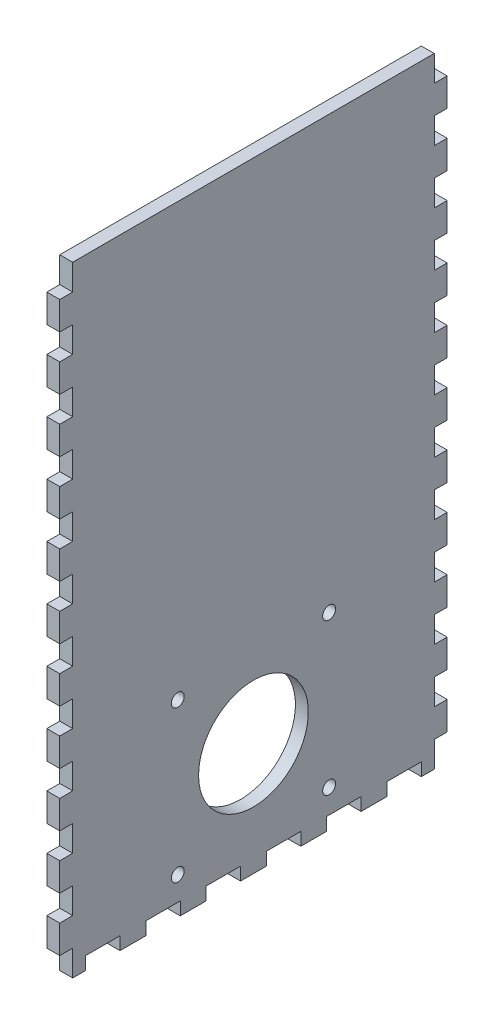
SolidWorks part; units mm, degrees
material "Acrylic (Medium-high impact)"
ref_plane "Front Plane" through (0, 0, 0) normal (0, 0, 1) x (1, 0, 0)
ref_plane "Top Plane" through (0, 0, 0) normal (0, 1, 0) x (1, 0, 0)
ref_plane "Right Plane" through (0, 0, 0) normal (1, 0, 0) x (0, 0, -1)
sketch "Sketch1" plane through (0, 0, 0) normal (0, 1, 0) x (1, 0, 0)
  line L1 (-254, 95.25) -> (254, 95.25)
  line L2 (-254, 95.25) -> (-254, -95.25)
  line L3 (-254, -95.25) -> (254, -95.25)
  line L4 (254, 95.25) -> (254, -95.25)
  point P4 (-254, 0)
  point P6 (0, 95.25)
  dimension "D1" = 190.5
  dimension "D2" = 508
extrude "Boss-Extrude1" add sketch "Sketch1" along normal blind 6.35
sketch "Sketch2" plane through (0, 6.35, 0) normal (0, 1, 0) x (1, 0, 0)
  line L0 (254, -95.25) -> (254, 95.25) construction
  line L1 (-254, 95.25) -> (254, 95.25)
  line L2 (-254, 95.25) -> (-254, -95.25)
  line L3 (-254, -95.25) -> (254, -95.25)
  line L4 (254, 95.25) -> (254, -95.25)
  line L5 (-254, -95.25) -> (254, -95.25) construction
  line L7 (-247.65, 88.9) -> (247.65, 88.9)
  line L8 (-247.65, 88.9) -> (-247.65, -88.9)
  line L9 (-247.65, -88.9) -> (247.65, -88.9)
  line L10 (247.65, 88.9) -> (247.65, -88.9)
  point P7 (-247.65, 0)
  point P14 (-254, 0)
  point P15 (0, -88.9)
  point P16 (0, -95.25)
  point P17 (247.65, 0)
  point P18 (254, 0)
  dimension "D1" = 6.35
  dimension "D2" = 6.35
extrude "Boss-Extrude2" add sketch "Sketch2" along normal blind 298.45
sketch "Sketch3" plane through (0, 0, 95.25) normal (0, 0, 1) x (1, 0, 0)
  line L0 (0, 304.8) -> (0, 0) construction
  line L1 (-254, 304.8) -> (254, 304.8) construction
  line L2 (-247.65, 6.35) -> (247.65, 6.35) construction
  line L4 (-3.302, 283.21) -> (-3.302, 6.35)
  line L5 (-3.302, 6.35) -> (3.302, 6.35)
  line L6 (3.302, 292.354) -> (3.302, 6.35)
  line L7 (3.302, 292.354) -> (-16.256, 292.354)
  line L9 (-5.842, 285.75) -> (-16.256, 285.75)
  line L10 (-16.256, 292.354) -> (-16.256, 285.75)
  line L11 (3.302, 101.6) -> (16.002, 101.6) construction
  line L12 (-254, 0) -> (254, 0) construction
  line L13 (12.827, 88.9) -> (12.827, 101.6) construction
  line L14 (9.652, 88.9) -> (16.002, 88.9)
  line L15 (9.652, 88.9) -> (9.652, 71.9667)
  line L16 (9.652, 71.9667) -> (16.002, 71.9667)
  line L17 (16.002, 88.9) -> (16.002, 71.9667)
  line L18 (9.652, 42.3333) -> (16.002, 42.3333)
  line L19 (9.652, 42.3333) -> (9.652, 59.2667)
  line L20 (9.652, 59.2667) -> (16.002, 59.2667)
  line L21 (16.002, 42.3333) -> (16.002, 59.2667)
  line L26 (9.652, 29.6333) -> (16.002, 29.6333)
  line L27 (9.652, 29.6333) -> (9.652, 12.7)
  line L28 (9.652, 12.7) -> (16.002, 12.7)
  line L29 (16.002, 29.6333) -> (16.002, 12.7)
  line L30 (12.827, 59.2667) -> (12.827, 71.9667) construction
  line L31 (12.827, 29.6333) -> (12.827, 42.3333) construction
  line L32 (12.827, 12.7) -> (12.827, 0) construction
  arc A0 (-3.302, 283.21) -> (-5.842, 285.75) centre (-5.842, 283.21) ccw
  point P5 (0, 6.35)
  dimension "D5" = 2.54
  dimension "D1" = 6.604
  dimension "D2" = 12.954
  dimension "D3" = 6.604
  dimension "D4" = 286.004
  dimension "D6" = 101.6
  dimension "D7" = 12.7
  dimension "D8" = 12.7
  dimension "D9" = 6.35
extrude "Cut-Extrude1" cut sketch "Sketch3" against normal blind 12.7
sketch "Sketch4" plane through (0, 0, -88.9) normal (0, 0, 1) x (1, 0, 0)
  line L0 (-254, 304.8) -> (254, 304.8) construction
  line L1 (-22.606, 304.8) -> (-16.256, 304.8)
  line L2 (-22.606, 304.8) -> (-22.606, 6.35)
  line L3 (-22.606, 6.35) -> (-16.256, 6.35)
  line L4 (-16.256, 304.8) -> (-16.256, 6.35)
  line L5 (6.477, 263.525) -> (6.477, 247.65) construction
  line L6 (-16.256, 292.354) -> (-16.256, 285.75) construction
  line L7 (3.302, 304.8) -> (9.652, 304.8)
  line L8 (3.302, 304.8) -> (3.302, 6.35)
  line L9 (3.302, 6.35) -> (9.652, 6.35)
  line L10 (9.652, 304.8) -> (9.652, 6.35)
  line L11 (247.65, 6.35) -> (-247.65, 6.35) construction
  line L12 (3.302, 6.35) -> (3.302, 292.354) construction
  line L13 (-16.256, 304.8) -> (-22.606, 304.8)
  line L14 (-16.256, 304.8) -> (-16.256, 292.1)
  line L15 (-16.256, 292.1) -> (-22.606, 292.1)
  line L16 (-22.606, 304.8) -> (-22.606, 292.1)
  line L17 (-16.256, 276.225) -> (-22.606, 276.225)
  line L18 (-16.256, 276.225) -> (-16.256, 263.525)
  line L19 (-16.256, 263.525) -> (-22.606, 263.525)
  line L20 (-22.606, 276.225) -> (-22.606, 263.525)
  line L21 (-22.606, 6.35) -> (-16.256, 6.35)
  line L22 (-22.606, 6.35) -> (-22.606, 19.05)
  line L23 (-22.606, 19.05) -> (-16.256, 19.05)
  line L24 (-16.256, 6.35) -> (-16.256, 19.05)
  line L25 (-22.606, 34.925) -> (-16.256, 34.925)
  line L26 (-22.606, 34.925) -> (-22.606, 47.625)
  line L27 (-22.606, 47.625) -> (-16.256, 47.625)
  line L28 (-16.256, 34.925) -> (-16.256, 47.625)
  line L29 (-22.606, 92.075) -> (-16.256, 92.075)
  line L30 (-22.606, 92.075) -> (-22.606, 104.775)
  line L31 (-22.606, 104.775) -> (-16.256, 104.775)
  line L32 (-16.256, 92.075) -> (-16.256, 104.775)
  line L33 (-22.606, 149.225) -> (-16.256, 149.225)
  line L34 (-22.606, 149.225) -> (-22.606, 161.925)
  line L35 (-22.606, 161.925) -> (-16.256, 161.925)
  line L36 (-16.256, 149.225) -> (-16.256, 161.925)
  line L37 (-22.606, 177.8) -> (-16.256, 177.8)
  line L38 (-22.606, 177.8) -> (-22.606, 190.5)
  line L39 (-22.606, 190.5) -> (-16.256, 190.5)
  line L40 (-16.256, 177.8) -> (-16.256, 190.5)
  line L41 (-22.606, 206.375) -> (-16.256, 206.375)
  line L42 (-22.606, 206.375) -> (-22.606, 219.075)
  line L43 (-22.606, 219.075) -> (-16.256, 219.075)
  line L44 (-16.256, 206.375) -> (-16.256, 219.075)
  line L45 (-22.606, 234.95) -> (-16.256, 234.95)
  line L46 (-22.606, 234.95) -> (-22.606, 247.65)
  line L47 (-22.606, 247.65) -> (-16.256, 247.65)
  line L48 (-16.256, 234.95) -> (-16.256, 247.65)
  line L49 (-16.256, 133.35) -> (-22.606, 133.35)
  line L50 (-16.256, 133.35) -> (-16.256, 120.65)
  line L51 (-16.256, 120.65) -> (-22.606, 120.65)
  line L52 (-22.606, 133.35) -> (-22.606, 120.65)
  line L53 (-16.256, 76.2) -> (-22.606, 76.2)
  line L54 (-16.256, 76.2) -> (-16.256, 63.5)
  line L55 (-16.256, 63.5) -> (-22.606, 63.5)
  line L56 (-22.606, 76.2) -> (-22.606, 63.5)
  line L57 (-19.431, 304.8) -> (-19.431, 292.1) construction
  line L58 (-19.431, 292.1) -> (-19.431, 276.225) construction
  line L59 (-19.431, 276.225) -> (-19.431, 263.525) construction
  line L60 (-19.431, 247.65) -> (-19.431, 234.95) construction
  line L61 (-19.431, 234.95) -> (-19.431, 219.075) construction
  line L62 (-19.431, 219.075) -> (-19.431, 206.375) construction
  line L63 (-19.431, 206.375) -> (-19.431, 190.5) construction
  line L64 (-19.431, 190.5) -> (-19.431, 177.8) construction
  line L65 (-19.431, 177.8) -> (-19.431, 161.925) construction
  line L66 (-19.431, 161.925) -> (-19.431, 149.225) construction
  line L67 (-19.431, 133.35) -> (-19.431, 120.65) construction
  line L68 (-19.431, 120.65) -> (-19.431, 104.775) construction
  line L69 (-19.431, 104.775) -> (-19.431, 92.075) construction
  line L70 (-19.431, 92.075) -> (-19.431, 76.2) construction
  line L71 (-19.431, 76.2) -> (-19.431, 63.5) construction
  line L72 (-19.431, 63.5) -> (-19.431, 47.625) construction
  line L73 (-19.431, 47.625) -> (-19.431, 34.925) construction
  line L74 (-19.431, 34.925) -> (-19.431, 19.05) construction
  line L75 (-19.431, 19.05) -> (-19.431, 6.35) construction
  line L76 (-19.431, 149.225) -> (-19.431, 133.35) construction
  line L77 (-19.431, 263.525) -> (-19.431, 247.65) construction
  line L78 (-6.477, 304.8) -> (-6.477, 0) construction
  line L79 (254, 304.8) -> (-254, 304.8) construction
  line L80 (254, 0) -> (-254, 0) construction
  line L81 (-6.477, 8.3493) -> (3.302, 8.3493) construction
  line L82 (-6.477, 8.3493) -> (-16.256, 8.3493) construction
  line L83 (6.477, 149.225) -> (6.477, 133.35) construction
  line L84 (6.477, 19.05) -> (6.477, 6.35) construction
  line L85 (6.477, 34.925) -> (6.477, 19.05) construction
  line L86 (6.477, 47.625) -> (6.477, 34.925) construction
  line L87 (6.477, 63.5) -> (6.477, 47.625) construction
  line L88 (6.477, 76.2) -> (6.477, 63.5) construction
  line L89 (6.477, 92.075) -> (6.477, 76.2) construction
  line L90 (6.477, 104.775) -> (6.477, 92.075) construction
  line L91 (6.477, 120.65) -> (6.477, 104.775) construction
  line L92 (6.477, 133.35) -> (6.477, 120.65) construction
  line L93 (6.477, 161.925) -> (6.477, 149.225) construction
  line L94 (6.477, 177.8) -> (6.477, 161.925) construction
  line L95 (6.477, 190.5) -> (6.477, 177.8) construction
  line L96 (6.477, 206.375) -> (6.477, 190.5) construction
  line L97 (6.477, 219.075) -> (6.477, 206.375) construction
  line L98 (6.477, 234.95) -> (6.477, 219.075) construction
  line L99 (6.477, 247.65) -> (6.477, 234.95) construction
  line L100 (6.477, 276.225) -> (6.477, 263.525) construction
  line L101 (6.477, 292.1) -> (6.477, 276.225) construction
  line L102 (6.477, 304.8) -> (6.477, 292.1) construction
  line L103 (9.652, 76.2) -> (9.652, 63.5)
  line L104 (3.302, 63.5) -> (9.652, 63.5)
  line L105 (3.302, 76.2) -> (3.302, 63.5)
  line L106 (3.302, 76.2) -> (9.652, 76.2)
  line L107 (9.652, 133.35) -> (9.652, 120.65)
  line L108 (3.302, 120.65) -> (9.652, 120.65)
  line L109 (3.302, 133.35) -> (3.302, 120.65)
  line L110 (3.302, 133.35) -> (9.652, 133.35)
  line L111 (3.302, 234.95) -> (3.302, 247.65)
  line L112 (9.652, 247.65) -> (3.302, 247.65)
  line L113 (9.652, 234.95) -> (9.652, 247.65)
  line L114 (9.652, 234.95) -> (3.302, 234.95)
  line L115 (3.302, 206.375) -> (3.302, 219.075)
  line L116 (9.652, 219.075) -> (3.302, 219.075)
  line L117 (9.652, 206.375) -> (9.652, 219.075)
  line L118 (9.652, 206.375) -> (3.302, 206.375)
  line L119 (3.302, 177.8) -> (3.302, 190.5)
  line L120 (9.652, 190.5) -> (3.302, 190.5)
  line L121 (9.652, 177.8) -> (9.652, 190.5)
  line L122 (9.652, 177.8) -> (3.302, 177.8)
  line L123 (3.302, 149.225) -> (3.302, 161.925)
  line L124 (9.652, 161.925) -> (3.302, 161.925)
  line L125 (9.652, 149.225) -> (9.652, 161.925)
  line L126 (9.652, 149.225) -> (3.302, 149.225)
  line L127 (3.302, 92.075) -> (3.302, 104.775)
  line L128 (9.652, 104.775) -> (3.302, 104.775)
  line L129 (9.652, 92.075) -> (9.652, 104.775)
  line L130 (9.652, 92.075) -> (3.302, 92.075)
  line L131 (3.302, 34.925) -> (3.302, 47.625)
  line L132 (9.652, 47.625) -> (3.302, 47.625)
  line L133 (9.652, 34.925) -> (9.652, 47.625)
  line L134 (9.652, 34.925) -> (3.302, 34.925)
  line L135 (3.302, 6.35) -> (3.302, 19.05)
  line L136 (9.652, 19.05) -> (3.302, 19.05)
  line L137 (9.652, 6.35) -> (9.652, 19.05)
  line L138 (9.652, 6.35) -> (3.302, 6.35)
  line L139 (9.652, 276.225) -> (9.652, 263.525)
  line L140 (3.302, 263.525) -> (9.652, 263.525)
  line L141 (3.302, 276.225) -> (3.302, 263.525)
  line L142 (3.302, 276.225) -> (9.652, 276.225)
  line L143 (9.652, 304.8) -> (9.652, 292.1)
  line L144 (3.302, 292.1) -> (9.652, 292.1)
  line L145 (3.302, 304.8) -> (3.302, 292.1)
  line L146 (3.302, 304.8) -> (9.652, 304.8)
  line L147 (3.302, 304.8) -> (3.302, 6.35)
  line L148 (9.652, 6.35) -> (3.302, 6.35)
  line L149 (9.652, 304.8) -> (9.652, 6.35)
  line L150 (9.652, 304.8) -> (3.302, 304.8)
  point P14 (-16.256, 289.052)
  dimension "D1" = 6.35
  dimension "D2" = 12.7
extrude "Cut-Extrude2" cut sketch "Sketch4" against normal up to next (6.35 mm away) contours L17 L4 L15 L2 | L2 L47 L4 L19 | L45 L2 L43 L4 | L41 L2 L39 L4 | L37 L2 L35 L4 | L49 L4 L33 L2 | L4 L51 L2 L31 | L53 L4 L29 L2 | L4 L55 L2 L27 | L25 L2 L23 L4
ref_plane "Plane1" through (-6.477, 0, 0) normal (-1, 0, 0) x (0, 0, 1)
mirror "Mirror1" about plane through (-6.477, 0, 0) normal (-1, 0, 0) of "Cut-Extrude2"
sketch "Sketch5" plane through (0, 0, 0) normal (0, -1, 0) x (-1, 0, 0)
  line L0 (-227.9316, -95.25) -> (-227.9316, -88.9)
  line L1 (-247.65, 88.9) -> (247.65, 88.9)
  line L2 (-247.65, 88.9) -> (-247.65, -88.9)
  line L3 (-247.65, -88.9) -> (247.65, -88.9)
  line L4 (247.65, 88.9) -> (247.65, -88.9)
  line L5 (-254, -95.25) -> (-241.3, -95.25)
  line L6 (-254, -95.25) -> (-254, -88.9)
  line L7 (-254, -88.9) -> (-241.3, -88.9)
  line L8 (-241.3, -95.25) -> (-241.3, -88.9)
  line L9 (-227.9316, -95.25) -> (-215.2316, -95.25)
  line L10 (-227.9316, -88.9) -> (-215.2316, -88.9)
  line L11 (-215.2316, -95.25) -> (-215.2316, -88.9)
  line L12 (-201.8632, -95.25) -> (-201.8632, -88.9)
  line L13 (-201.8632, -95.25) -> (-189.1632, -95.25)
  line L14 (-201.8632, -88.9) -> (-189.1632, -88.9)
  line L15 (-189.1632, -95.25) -> (-189.1632, -88.9)
  line L16 (-175.7947, -95.25) -> (-175.7947, -88.9)
  line L17 (-175.7947, -95.25) -> (-163.0947, -95.25)
  line L18 (-175.7947, -88.9) -> (-163.0947, -88.9)
  line L19 (-163.0947, -95.25) -> (-163.0947, -88.9)
  line L20 (-149.7263, -95.25) -> (-149.7263, -88.9)
  line L21 (-149.7263, -95.25) -> (-137.0263, -95.25)
  line L22 (-149.7263, -88.9) -> (-137.0263, -88.9)
  line L23 (-137.0263, -95.25) -> (-137.0263, -88.9)
  line L24 (-123.6579, -95.25) -> (-123.6579, -88.9)
  line L25 (-123.6579, -95.25) -> (-110.9579, -95.25)
  line L26 (-123.6579, -88.9) -> (-110.9579, -88.9)
  line L27 (-110.9579, -95.25) -> (-110.9579, -88.9)
  line L28 (-97.5895, -95.25) -> (-97.5895, -88.9)
  line L29 (-97.5895, -95.25) -> (-84.8895, -95.25)
  line L30 (-97.5895, -88.9) -> (-84.8895, -88.9)
  line L31 (-84.8895, -95.25) -> (-84.8895, -88.9)
  line L32 (-71.5211, -95.25) -> (-71.5211, -88.9)
  line L33 (-71.5211, -95.25) -> (-58.8211, -95.25)
  line L34 (-71.5211, -88.9) -> (-58.8211, -88.9)
  line L35 (-58.8211, -95.25) -> (-58.8211, -88.9)
  line L36 (-45.4526, -95.25) -> (-45.4526, -88.9)
  line L37 (-45.4526, -95.25) -> (-32.7526, -95.25)
  line L38 (-45.4526, -88.9) -> (-32.7526, -88.9)
  line L39 (-32.7526, -95.25) -> (-32.7526, -88.9)
  line L40 (-19.3842, -95.25) -> (-19.3842, -88.9)
  line L41 (-19.3842, -95.25) -> (-6.6842, -95.25)
  line L42 (-19.3842, -88.9) -> (-6.6842, -88.9)
  line L43 (-6.6842, -95.25) -> (-6.6842, -88.9)
  line L44 (6.6842, -95.25) -> (6.6842, -88.9)
  line L45 (6.6842, -95.25) -> (19.3842, -95.25)
  line L46 (6.6842, -88.9) -> (19.3842, -88.9)
  line L47 (19.3842, -95.25) -> (19.3842, -88.9)
  line L48 (32.7526, -95.25) -> (32.7526, -88.9)
  line L49 (32.7526, -95.25) -> (45.4526, -95.25)
  line L50 (32.7526, -88.9) -> (45.4526, -88.9)
  line L51 (45.4526, -95.25) -> (45.4526, -88.9)
  line L52 (58.8211, -95.25) -> (58.8211, -88.9)
  line L53 (58.8211, -95.25) -> (71.5211, -95.25)
  line L54 (58.8211, -88.9) -> (71.5211, -88.9)
  line L55 (71.5211, -95.25) -> (71.5211, -88.9)
  line L56 (84.8895, -95.25) -> (84.8895, -88.9)
  line L57 (84.8895, -95.25) -> (97.5895, -95.25)
  line L58 (84.8895, -88.9) -> (97.5895, -88.9)
  line L59 (97.5895, -95.25) -> (97.5895, -88.9)
  line L60 (110.9579, -95.25) -> (110.9579, -88.9)
  line L61 (110.9579, -95.25) -> (123.6579, -95.25)
  line L62 (110.9579, -88.9) -> (123.6579, -88.9)
  line L63 (123.6579, -95.25) -> (123.6579, -88.9)
  line L64 (137.0263, -95.25) -> (137.0263, -88.9)
  line L65 (137.0263, -95.25) -> (149.7263, -95.25)
  line L66 (137.0263, -88.9) -> (149.7263, -88.9)
  line L67 (149.7263, -95.25) -> (149.7263, -88.9)
  line L68 (163.0947, -95.25) -> (163.0947, -88.9)
  line L69 (163.0947, -95.25) -> (175.7947, -95.25)
  line L70 (163.0947, -88.9) -> (175.7947, -88.9)
  line L71 (175.7947, -95.25) -> (175.7947, -88.9)
  line L72 (189.1632, -95.25) -> (189.1632, -88.9)
  line L73 (189.1632, -95.25) -> (201.8632, -95.25)
  line L74 (189.1632, -88.9) -> (201.8632, -88.9)
  line L75 (201.8632, -95.25) -> (201.8632, -88.9)
  line L76 (215.2316, -95.25) -> (215.2316, -88.9)
  line L77 (215.2316, -95.25) -> (227.9316, -95.25)
  line L78 (215.2316, -88.9) -> (227.9316, -88.9)
  line L79 (227.9316, -95.25) -> (227.9316, -88.9)
  line L80 (241.3, -95.25) -> (241.3, -88.9)
  line L81 (241.3, -95.25) -> (254, -95.25)
  line L82 (241.3, -88.9) -> (254, -88.9)
  line L83 (254, -95.25) -> (254, -88.9)
  line L84 (-167.64, 0) -> (167.64, 0) construction
  line L85 (254, 95.25) -> (254, 88.9)
  line L86 (241.3, 88.9) -> (254, 88.9)
  line L87 (241.3, 95.25) -> (254, 95.25)
  line L88 (241.3, 95.25) -> (241.3, 88.9)
  line L89 (227.9316, 95.25) -> (227.9316, 88.9)
  line L90 (215.2316, 88.9) -> (227.9316, 88.9)
  line L91 (215.2316, 95.25) -> (227.9316, 95.25)
  line L92 (215.2316, 95.25) -> (215.2316, 88.9)
  line L93 (201.8632, 95.25) -> (201.8632, 88.9)
  line L94 (189.1632, 88.9) -> (201.8632, 88.9)
  line L95 (189.1632, 95.25) -> (201.8632, 95.25)
  line L96 (189.1632, 95.25) -> (189.1632, 88.9)
  line L97 (175.7947, 95.25) -> (175.7947, 88.9)
  line L98 (163.0947, 88.9) -> (175.7947, 88.9)
  line L99 (163.0947, 95.25) -> (175.7947, 95.25)
  line L100 (163.0947, 95.25) -> (163.0947, 88.9)
  line L101 (149.7263, 95.25) -> (149.7263, 88.9)
  line L102 (137.0263, 88.9) -> (149.7263, 88.9)
  line L103 (137.0263, 95.25) -> (149.7263, 95.25)
  line L104 (137.0263, 95.25) -> (137.0263, 88.9)
  line L105 (123.6579, 95.25) -> (123.6579, 88.9)
  line L106 (110.9579, 88.9) -> (123.6579, 88.9)
  line L107 (110.9579, 95.25) -> (123.6579, 95.25)
  line L108 (110.9579, 95.25) -> (110.9579, 88.9)
  line L109 (97.5895, 95.25) -> (97.5895, 88.9)
  line L110 (84.8895, 88.9) -> (97.5895, 88.9)
  line L111 (84.8895, 95.25) -> (97.5895, 95.25)
  line L112 (84.8895, 95.25) -> (84.8895, 88.9)
  line L113 (71.5211, 95.25) -> (71.5211, 88.9)
  line L114 (58.8211, 88.9) -> (71.5211, 88.9)
  line L115 (58.8211, 95.25) -> (71.5211, 95.25)
  line L116 (58.8211, 95.25) -> (58.8211, 88.9)
  line L117 (45.4526, 95.25) -> (45.4526, 88.9)
  line L118 (32.7526, 88.9) -> (45.4526, 88.9)
  line L119 (32.7526, 95.25) -> (45.4526, 95.25)
  line L120 (32.7526, 95.25) -> (32.7526, 88.9)
  line L121 (19.3842, 95.25) -> (19.3842, 88.9)
  line L122 (6.6842, 88.9) -> (19.3842, 88.9)
  line L123 (6.6842, 95.25) -> (19.3842, 95.25)
  line L124 (6.6842, 95.25) -> (6.6842, 88.9)
  line L125 (-6.6842, 95.25) -> (-6.6842, 88.9)
  line L126 (-19.3842, 88.9) -> (-6.6842, 88.9)
  line L127 (-19.3842, 95.25) -> (-6.6842, 95.25)
  line L128 (-19.3842, 95.25) -> (-19.3842, 88.9)
  line L129 (-32.7526, 95.25) -> (-32.7526, 88.9)
  line L130 (-45.4526, 88.9) -> (-32.7526, 88.9)
  line L131 (-45.4526, 95.25) -> (-32.7526, 95.25)
  line L132 (-45.4526, 95.25) -> (-45.4526, 88.9)
  line L133 (-58.8211, 95.25) -> (-58.8211, 88.9)
  line L134 (-71.5211, 88.9) -> (-58.8211, 88.9)
  line L135 (-71.5211, 95.25) -> (-58.8211, 95.25)
  line L136 (-71.5211, 95.25) -> (-71.5211, 88.9)
  line L137 (-84.8895, 95.25) -> (-84.8895, 88.9)
  line L138 (-97.5895, 88.9) -> (-84.8895, 88.9)
  line L139 (-97.5895, 95.25) -> (-84.8895, 95.25)
  line L140 (-97.5895, 95.25) -> (-97.5895, 88.9)
  line L141 (-110.9579, 95.25) -> (-110.9579, 88.9)
  line L142 (-123.6579, 88.9) -> (-110.9579, 88.9)
  line L143 (-123.6579, 95.25) -> (-110.9579, 95.25)
  line L144 (-123.6579, 95.25) -> (-123.6579, 88.9)
  line L145 (-137.0263, 95.25) -> (-137.0263, 88.9)
  line L146 (-149.7263, 88.9) -> (-137.0263, 88.9)
  line L147 (-149.7263, 95.25) -> (-137.0263, 95.25)
  line L148 (-149.7263, 95.25) -> (-149.7263, 88.9)
  line L149 (-163.0947, 95.25) -> (-163.0947, 88.9)
  line L150 (-175.7947, 88.9) -> (-163.0947, 88.9)
  line L151 (-175.7947, 95.25) -> (-163.0947, 95.25)
  line L152 (-175.7947, 95.25) -> (-175.7947, 88.9)
  line L153 (-189.1632, 95.25) -> (-189.1632, 88.9)
  line L154 (-201.8632, 88.9) -> (-189.1632, 88.9)
  line L155 (-201.8632, 95.25) -> (-189.1632, 95.25)
  line L156 (-201.8632, 95.25) -> (-201.8632, 88.9)
  line L157 (-215.2316, 95.25) -> (-215.2316, 88.9)
  line L158 (-227.9316, 88.9) -> (-215.2316, 88.9)
  line L159 (-227.9316, 95.25) -> (-215.2316, 95.25)
  line L160 (-241.3, 95.25) -> (-241.3, 88.9)
  line L161 (-254, 88.9) -> (-241.3, 88.9)
  line L162 (-254, 95.25) -> (-254, 88.9)
  line L163 (-254, 95.25) -> (-241.3, 95.25)
  line L164 (-247.65, 88.9) -> (247.65, 88.9)
  line L165 (-227.9316, 95.25) -> (-227.9316, 88.9)
  line L166 (-254, 65.6167) -> (-254, 52.9167)
  line L167 (-254, 95.25) -> (-247.65, 95.25)
  line L168 (-254, 95.25) -> (-254, 82.55)
  line L169 (-254, 82.55) -> (-247.65, 82.55)
  line L170 (-247.65, 95.25) -> (-247.65, 82.55)
  line L171 (-254, 65.6167) -> (-247.65, 65.6167)
  line L172 (-247.65, 65.6167) -> (-247.65, 52.9167)
  line L173 (-254, 52.9167) -> (-247.65, 52.9167)
  line L174 (-254, 35.9833) -> (-254, 23.2833)
  line L175 (-254, 35.9833) -> (-247.65, 35.9833)
  line L176 (-247.65, 35.9833) -> (-247.65, 23.2833)
  line L177 (-254, 23.2833) -> (-247.65, 23.2833)
  line L178 (-254, 6.35) -> (-254, -6.35)
  line L179 (-254, 6.35) -> (-247.65, 6.35)
  line L180 (-247.65, 6.35) -> (-247.65, -6.35)
  line L181 (-254, -6.35) -> (-247.65, -6.35)
  line L182 (-254, -23.2833) -> (-254, -35.9833)
  line L183 (-254, -23.2833) -> (-247.65, -23.2833)
  line L184 (-247.65, -23.2833) -> (-247.65, -35.9833)
  line L185 (-254, -35.9833) -> (-247.65, -35.9833)
  line L186 (-254, -52.9167) -> (-254, -65.6167)
  line L187 (-254, -52.9167) -> (-247.65, -52.9167)
  line L188 (-247.65, -52.9167) -> (-247.65, -65.6167)
  line L189 (-254, -65.6167) -> (-247.65, -65.6167)
  line L190 (-254, -82.55) -> (-254, -95.25)
  line L191 (-254, -82.55) -> (-247.65, -82.55)
  line L192 (-247.65, -82.55) -> (-247.65, -95.25)
  line L193 (-254, -95.25) -> (-247.65, -95.25)
  line L194 (0, 104.775) -> (0, -104.775) construction
  line L195 (254, -95.25) -> (247.65, -95.25)
  line L196 (247.65, -82.55) -> (247.65, -95.25)
  line L197 (254, -82.55) -> (247.65, -82.55)
  line L198 (254, -82.55) -> (254, -95.25)
  line L199 (254, -65.6167) -> (247.65, -65.6167)
  line L200 (247.65, -52.9167) -> (247.65, -65.6167)
  line L201 (254, -52.9167) -> (247.65, -52.9167)
  line L202 (254, -52.9167) -> (254, -65.6167)
  line L203 (254, -35.9833) -> (247.65, -35.9833)
  line L204 (247.65, -23.2833) -> (247.65, -35.9833)
  line L205 (254, -23.2833) -> (247.65, -23.2833)
  line L206 (254, -23.2833) -> (254, -35.9833)
  line L207 (254, -6.35) -> (247.65, -6.35)
  line L208 (247.65, 6.35) -> (247.65, -6.35)
  line L209 (254, 6.35) -> (247.65, 6.35)
  line L210 (254, 6.35) -> (254, -6.35)
  line L211 (254, 23.2833) -> (247.65, 23.2833)
  line L212 (247.65, 35.9833) -> (247.65, 23.2833)
  line L213 (254, 35.9833) -> (247.65, 35.9833)
  line L214 (254, 35.9833) -> (254, 23.2833)
  line L215 (254, 52.9167) -> (247.65, 52.9167)
  line L216 (247.65, 65.6167) -> (247.65, 52.9167)
  line L217 (254, 65.6167) -> (247.65, 65.6167)
  line L218 (247.65, 95.25) -> (247.65, 82.55)
  line L219 (254, 82.55) -> (247.65, 82.55)
  line L220 (254, 95.25) -> (254, 82.55)
  line L221 (254, 95.25) -> (247.65, 95.25)
  line L222 (254, 65.6167) -> (254, 52.9167)
  line L223 (254, 95.25) -> (254, 88.9)
  line L224 (254, -95.25) -> (254, -88.9)
  line L225 (247.65, 88.9) -> (247.65, -88.9)
  line M114 (254, -95.25) -> (254, 95.25)
  dimension "D1" = 12.7
  dimension "D3" = 6.35
  dimension "D5" = 12.7
  dimension "D2" = 20
  dimension "D4" = 7
sketch "Sketch6" plane through (0, 0, 0) normal (0, 1, 0) x (1, 0, 0)
  line L1 (-247.65, 117.4399) -> (267.1511, 117.4399)
  line L2 (-247.65, 117.4399) -> (-247.65, -137.4416)
  line L3 (-247.65, -137.4416) -> (267.1511, -137.4416)
  line L4 (267.1511, 117.4399) -> (267.1511, -137.4416)
  line L6 (-247.65, 88.9) -> (-247.65, -88.9) construction
extrude "Cut-Extrude5" cut sketch "Sketch6" along normal through all
extrude "Cut-Extrude6" cut sketch "Sketch5" against normal blind 6.35 contours L199 L4 L197 M114 | L203 L4 L201 M114 | L207 L4 L205 M114 | L211 L4 L209 M114 | L215 L4 L213 M114 | L219 L4 L217 M114
sketch "Sketch7" plane through (-254, 0, 0) normal (-1, 0, 0) x (0, 0, 1)
  line L0 (-95.25, 26.5545) -> (-95.25, 39.2545)
  line L1 (-95.25, 0) -> (-88.9, 0)
  line L2 (-95.25, 0) -> (-95.25, 12.7)
  line L3 (-95.25, 12.7) -> (-88.9, 12.7)
  line L4 (-88.9, 0) -> (-88.9, 12.7)
  line L5 (-95.25, 39.2545) -> (-88.9, 39.2545)
  line L6 (-88.9, 26.5545) -> (-88.9, 39.2545)
  line L7 (-95.25, 26.5545) -> (-88.9, 26.5545)
  line L8 (-95.25, 53.1091) -> (-95.25, 65.8091)
  line L9 (-95.25, 65.8091) -> (-88.9, 65.8091)
  line L10 (-88.9, 53.1091) -> (-88.9, 65.8091)
  line L11 (-95.25, 53.1091) -> (-88.9, 53.1091)
  line L12 (-95.25, 79.6636) -> (-95.25, 92.3636)
  line L13 (-95.25, 92.3636) -> (-88.9, 92.3636)
  line L14 (-88.9, 79.6636) -> (-88.9, 92.3636)
  line L15 (-95.25, 79.6636) -> (-88.9, 79.6636)
  line L16 (-95.25, 106.2182) -> (-95.25, 118.9182)
  line L17 (-95.25, 118.9182) -> (-88.9, 118.9182)
  line L18 (-88.9, 106.2182) -> (-88.9, 118.9182)
  line L19 (-95.25, 106.2182) -> (-88.9, 106.2182)
  line L20 (-95.25, 132.7727) -> (-95.25, 145.4727)
  line L21 (-95.25, 145.4727) -> (-88.9, 145.4727)
  line L22 (-88.9, 132.7727) -> (-88.9, 145.4727)
  line L23 (-95.25, 132.7727) -> (-88.9, 132.7727)
  line L24 (-95.25, 159.3273) -> (-95.25, 172.0273)
  line L25 (-95.25, 172.0273) -> (-88.9, 172.0273)
  line L26 (-88.9, 159.3273) -> (-88.9, 172.0273)
  line L27 (-95.25, 159.3273) -> (-88.9, 159.3273)
  line L28 (-95.25, 185.8818) -> (-95.25, 198.5818)
  line L29 (-95.25, 198.5818) -> (-88.9, 198.5818)
  line L30 (-88.9, 185.8818) -> (-88.9, 198.5818)
  line L31 (-95.25, 185.8818) -> (-88.9, 185.8818)
  line L32 (-95.25, 212.4364) -> (-95.25, 225.1364)
  line L33 (-95.25, 225.1364) -> (-88.9, 225.1364)
  line L34 (-88.9, 212.4364) -> (-88.9, 225.1364)
  line L35 (-95.25, 212.4364) -> (-88.9, 212.4364)
  line L36 (-95.25, 238.9909) -> (-95.25, 251.6909)
  line L37 (-95.25, 251.6909) -> (-88.9, 251.6909)
  line L38 (-88.9, 238.9909) -> (-88.9, 251.6909)
  line L39 (-95.25, 238.9909) -> (-88.9, 238.9909)
  line L40 (-95.25, 265.5455) -> (-95.25, 278.2455)
  line L41 (-95.25, 278.2455) -> (-88.9, 278.2455)
  line L42 (-88.9, 265.5455) -> (-88.9, 278.2455)
  line L43 (-95.25, 265.5455) -> (-88.9, 265.5455)
  line L44 (-95.25, 292.1) -> (-95.25, 304.8)
  line L45 (-95.25, 304.8) -> (-88.9, 304.8)
  line L46 (-88.9, 292.1) -> (-88.9, 304.8)
  line L47 (-95.25, 292.1) -> (-88.9, 292.1)
  line L48 (0, -3.4925) -> (0, 3.4925) construction
  line L49 (95.25, 292.1) -> (88.9, 292.1)
  line L50 (88.9, 292.1) -> (88.9, 304.8)
  line L51 (95.25, 304.8) -> (88.9, 304.8)
  line L52 (95.25, 292.1) -> (95.25, 304.8)
  line L53 (95.25, 265.5455) -> (88.9, 265.5455)
  line L54 (88.9, 265.5455) -> (88.9, 278.2455)
  line L55 (95.25, 278.2455) -> (88.9, 278.2455)
  line L56 (95.25, 265.5455) -> (95.25, 278.2455)
  line L57 (95.25, 238.9909) -> (88.9, 238.9909)
  line L58 (88.9, 238.9909) -> (88.9, 251.6909)
  line L59 (95.25, 251.6909) -> (88.9, 251.6909)
  line L60 (95.25, 238.9909) -> (95.25, 251.6909)
  line L61 (95.25, 212.4364) -> (88.9, 212.4364)
  line L62 (88.9, 212.4364) -> (88.9, 225.1364)
  line L63 (95.25, 225.1364) -> (88.9, 225.1364)
  line L64 (95.25, 212.4364) -> (95.25, 225.1364)
  line L65 (95.25, 185.8818) -> (88.9, 185.8818)
  line L66 (88.9, 185.8818) -> (88.9, 198.5818)
  line L67 (95.25, 198.5818) -> (88.9, 198.5818)
  line L68 (95.25, 185.8818) -> (95.25, 198.5818)
  line L69 (95.25, 159.3273) -> (88.9, 159.3273)
  line L70 (88.9, 159.3273) -> (88.9, 172.0273)
  line L71 (95.25, 172.0273) -> (88.9, 172.0273)
  line L72 (95.25, 159.3273) -> (95.25, 172.0273)
  line L73 (95.25, 132.7727) -> (88.9, 132.7727)
  line L74 (88.9, 132.7727) -> (88.9, 145.4727)
  line L75 (95.25, 145.4727) -> (88.9, 145.4727)
  line L76 (95.25, 132.7727) -> (95.25, 145.4727)
  line L77 (95.25, 106.2182) -> (88.9, 106.2182)
  line L78 (88.9, 106.2182) -> (88.9, 118.9182)
  line L79 (95.25, 118.9182) -> (88.9, 118.9182)
  line L80 (95.25, 106.2182) -> (95.25, 118.9182)
  line L81 (95.25, 79.6636) -> (88.9, 79.6636)
  line L82 (88.9, 79.6636) -> (88.9, 92.3636)
  line L83 (95.25, 92.3636) -> (88.9, 92.3636)
  line L84 (95.25, 79.6636) -> (95.25, 92.3636)
  line L85 (95.25, 53.1091) -> (88.9, 53.1091)
  line L86 (88.9, 53.1091) -> (88.9, 65.8091)
  line L87 (95.25, 65.8091) -> (88.9, 65.8091)
  line L88 (95.25, 53.1091) -> (95.25, 65.8091)
  line L89 (95.25, 26.5545) -> (88.9, 26.5545)
  line L90 (88.9, 26.5545) -> (88.9, 39.2545)
  line L91 (95.25, 39.2545) -> (88.9, 39.2545)
  line L92 (88.9, 0) -> (88.9, 12.7)
  line L93 (95.25, 12.7) -> (88.9, 12.7)
  line L94 (95.25, 0) -> (95.25, 12.7)
  line L95 (95.25, 0) -> (88.9, 0)
  line L96 (95.25, 26.5545) -> (95.25, 39.2545)
  dimension "D1" = 12.7
  dimension "D2" = 6.35
  dimension "D3" = 12
extrude "Cut-Extrude7" cut sketch "Sketch7" against normal through all
sketch "Sketch8" plane through (-254, 0, 0) normal (-1, 0, 0) x (0, 0, 1)
  line L1 (-37.211, 92.583) -> (37.211, 92.583)
  line L2 (-37.211, 92.583) -> (-37.211, 18.161)
  line L3 (-37.211, 18.161) -> (37.211, 18.161)
  line L4 (37.211, 92.583) -> (37.211, 18.161)
  circle A0 centre (0, 55.372) radius 26.9875
  circle A1 centre (-37.211, 92.583) radius 3.175
  circle A2 centre (37.211, 92.583) radius 3.175
  circle A3 centre (-37.211, 18.161) radius 3.175
  circle A4 centre (37.211, 18.161) radius 3.175
  point P15 (0, 18.161)
  point P18 (-37.211, 55.372)
  dimension "D1" = 53.975
  dimension "D2" = 6.35
  dimension "D3" = 74.422
  dimension "D4" = 55.372
extrude "Cut-Extrude8" cut sketch "Sketch8" against normal through all contours A0 | A1 | A2 | A4 | A3
